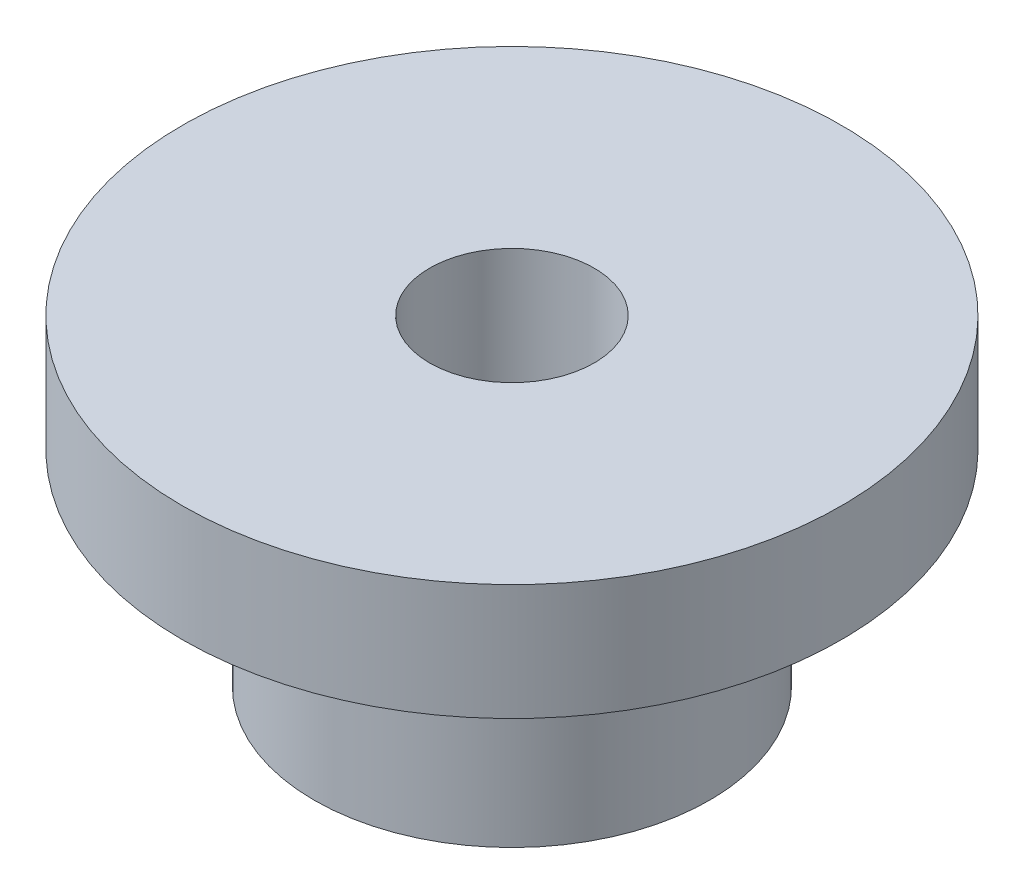
SolidWorks part; units mm, degrees
ref_plane "Front Plane" through (0, 0, 0) normal (0, 0, 1) x (1, 0, 0)
ref_plane "Top Plane" through (0, 0, 0) normal (0, 1, 0) x (1, 0, 0)
ref_plane "Right Plane" through (0, 0, 0) normal (1, 0, 0) x (0, 0, -1)
sketch "Sketch1" plane through (0, 0, 0) normal (0, 1, 0) x (1, 0, 0)
  circle A0 centre (0, 0) radius 4.7625
  circle A1 centre (0, 0) radius 1.9812
  dimension "D1" = 9.525
  dimension "D2" = 3.9624
extrude "Extrude1" add sketch "Sketch1" along normal blind 4.9352
sketch "Sketch2" plane through (0, 4.9352, 0) normal (0, 1, 0) x (-1, 0, 0)
  line L0 (0, 0) -> (84.0079, 0) construction
  circle A0 centre (0, 0) radius 7.9375
  circle A1 centre (0, 0) radius 1.9812 construction
  circle A2 centre (0, 0) radius 1.9812
  dimension "D1" = 15.875
extrude "Extrude2" add sketch "Sketch2" along normal blind 2.794
split "Split1"
